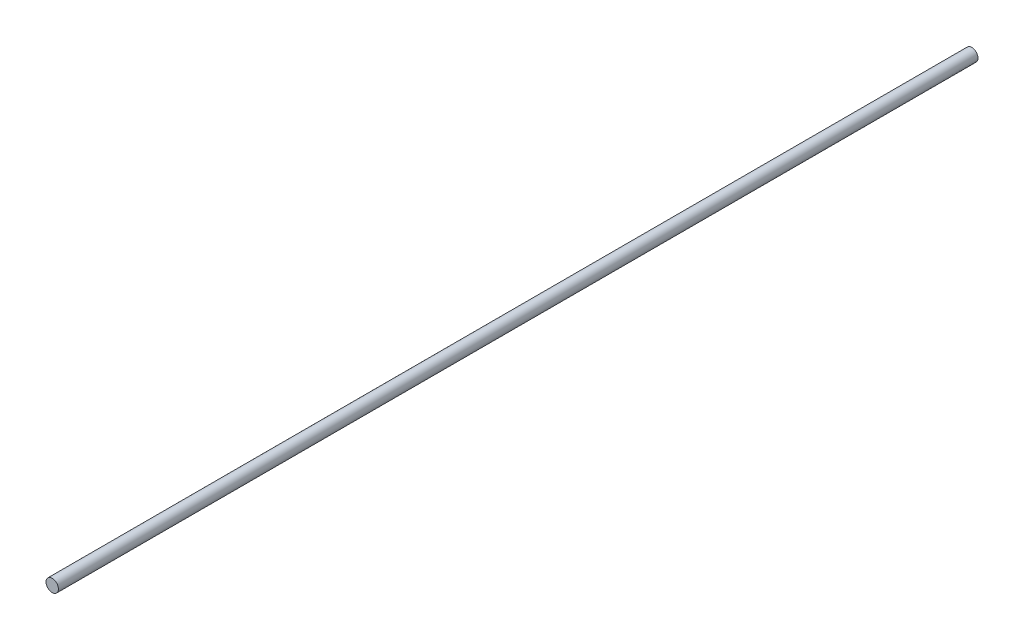
SolidWorks part; units mm, degrees
ref_plane "Front Plane" through (0, 0, 0) normal (0, 0, 1) x (1, 0, 0)
ref_plane "Top Plane" through (0, 0, 0) normal (0, 1, 0) x (1, 0, 0)
ref_plane "Right Plane" through (0, 0, 0) normal (1, 0, 0) x (0, 0, -1)
sketch "Sketch1" plane through (0, 0, 0) normal (0, 0, 1) x (1, 0, 0)
  circle A0 centre (0, 0) radius 2.5
  dimension "D1" = 5
extrude "Boss-Extrude1" add sketch "Sketch1" along normal blind 370
